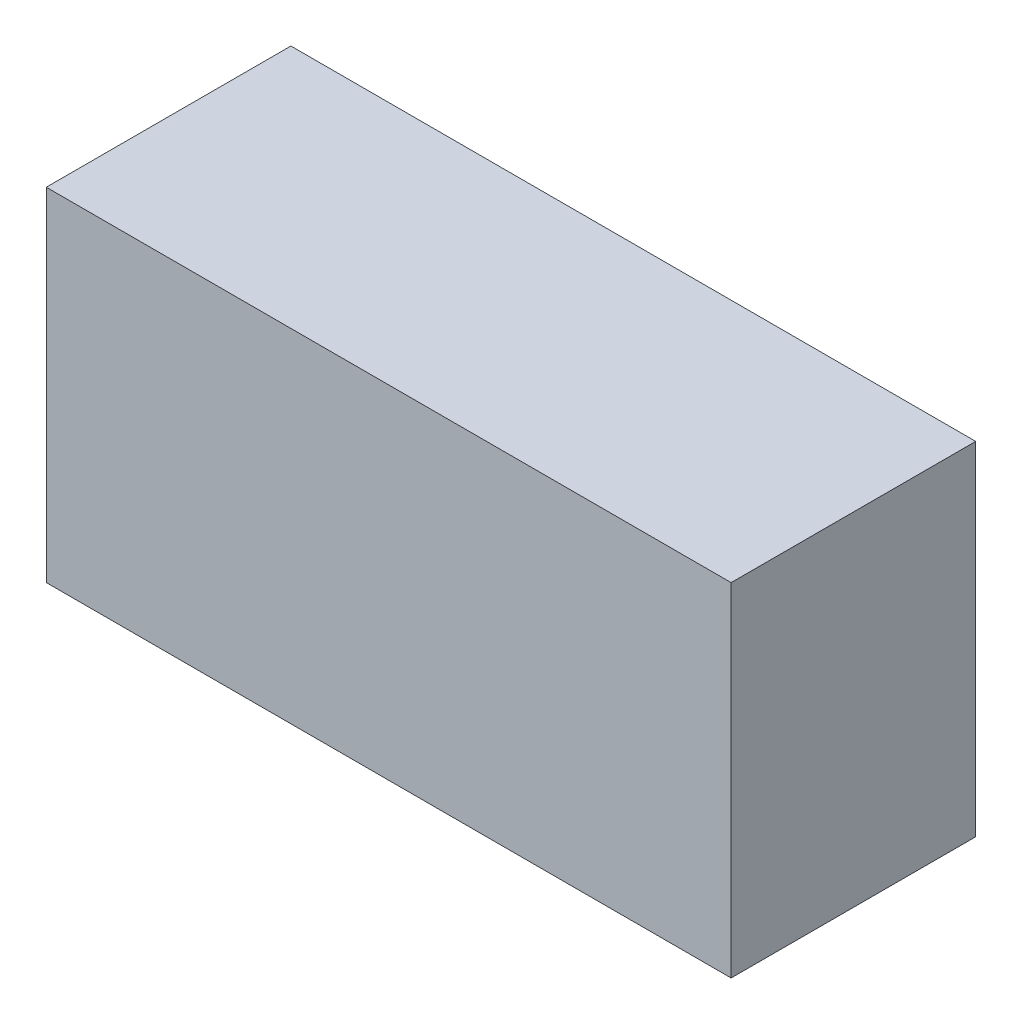
SolidWorks part; units mm, degrees
ref_plane "Plan de face" through (0, 0, 0) normal (0, 0, 1) x (1, 0, 0)
ref_plane "Plan de dessus" through (0, 0, 0) normal (0, 1, 0) x (1, 0, 0)
ref_plane "Plan de droite" through (0, 0, 0) normal (1, 0, 0) x (0, 0, -1)
sketch "Esquisse1" plane through (0, 0, 0) normal (0, 0, 1) x (1, 0, 0)
  line L1 (0, 0) -> (70, 0)
  line L2 (0, 0) -> (0, 35)
  line L3 (0, 35) -> (70, 35)
  line L4 (70, 0) -> (70, 35)
  dimension "D1" = 70
  dimension "D2" = 35
extrude "Boss.-Extru.1" add sketch "Esquisse1" along normal blind 25
